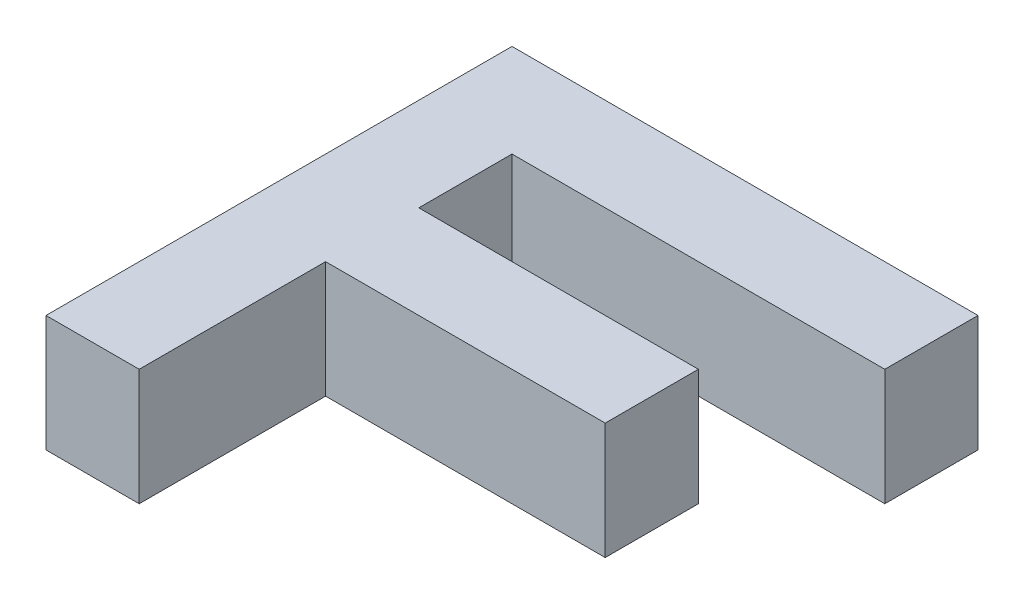
SolidWorks part; units mm, degrees
ref_plane "Front Plane" through (0, 0, 0) normal (0, 0, 1) x (1, 0, 0)
ref_plane "Top Plane" through (0, 0, 0) normal (0, 1, 0) x (1, 0, 0)
ref_plane "Right Plane" through (0, 0, 0) normal (1, 0, 0) x (0, 0, -1)
sketch "Sketch1" plane through (0, 0, 0) normal (0, 1, 0) x (1, 0, 0)
  line L0 (250, 0) -> (250, 40)
  line L1 (250, 40) -> (290, 40)
  line L2 (290, 40) -> (290, 32)
  line L3 (290, 32) -> (258, 32)
  line L4 (258, 32) -> (258, 24)
  line L5 (258, 24) -> (282, 24)
  line L6 (282, 24) -> (282, 16)
  line L7 (282, 16) -> (258, 16)
  line L8 (258, 16) -> (258, 0)
  line L9 (258, 0) -> (250, 0)
  dimension "D1" = 250
  dimension "D2" = 40
  dimension "D3" = 40
  dimension "D4" = 8
  dimension "D5" = 8
  dimension "D6" = 8
  dimension "D7" = 8
  dimension "D8" = 8
extrude "Boss-Extrude1" add sketch "Sketch1" along normal blind 10
